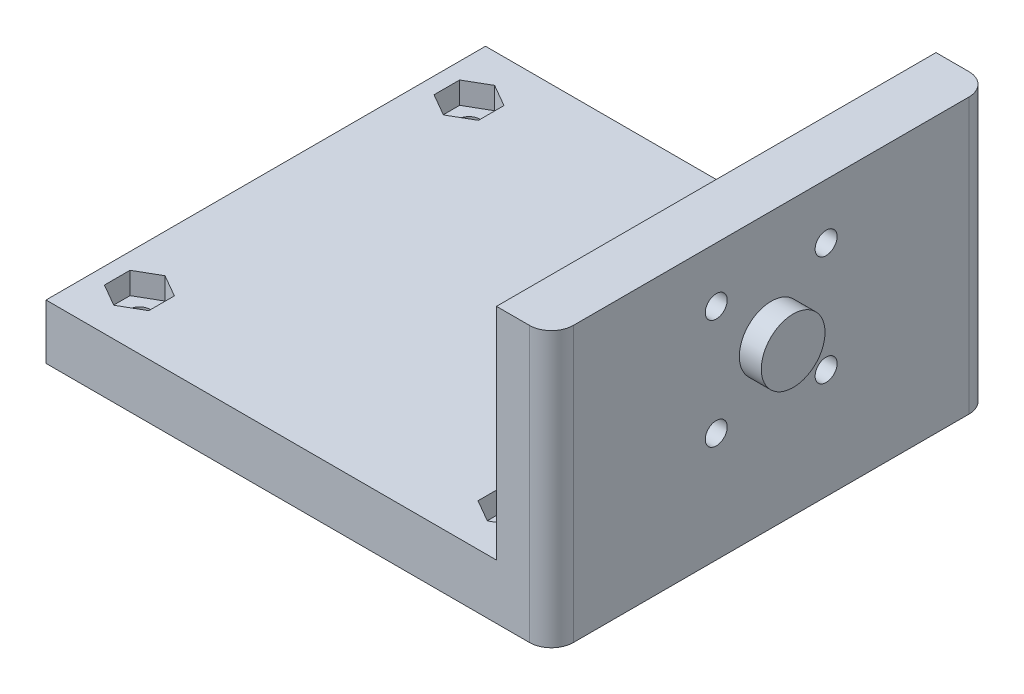
SolidWorks part; units mm, degrees
ref_plane "Plan de face" through (0, 0, 0) normal (0, 0, 1) x (1, 0, 0)
ref_plane "Plan de dessus" through (0, 0, 0) normal (0, 1, 0) x (1, 0, 0)
ref_plane "Plan de droite" through (0, 0, 0) normal (1, 0, 0) x (0, 0, -1)
sketch "Esquisse1" plane through (0, 0, 0) normal (0, 1, 0) x (1, 0, 0)
  line L1 (0, 20) -> (-5, 20)
  line L2 (0, 20) -> (0, -20)
  line L3 (0, -20) -> (-5, -20)
  line L4 (-5, 20) -> (-5, -20)
  dimension "D1" = 5
  dimension "D2" = 40
  dimension "D3" = 20
extrude "Boss.-Extru.1" add sketch "Esquisse1" against normal blind 25
sketch "Esquisse2" plane through (-5, 0, 0) normal (-1, 0, 0) x (0, 0, 1)
  line L0 (-20, -25) -> (-20, 0) construction
  line L1 (20, -25) -> (-20, -25)
  line L2 (20, -25) -> (20, -20)
  line L3 (20, -20) -> (-20, -20)
  line L4 (-20, -25) -> (-20, -20)
  dimension "D1" = 5
extrude "Boss.-Extru.2" add sketch "Esquisse2" along normal blind 41
fillet "Congé1" radius 2 2 edges at (0, -12.5, -20) (0, -12.5, 20)
sketch "Esquisse4" plane through (0, 0, 0) normal (1, 0, 0) x (0, 0, -1)
  circle A0 centre (-5, -5) radius 1
  circle A1 centre (5, -5) radius 1
  circle A2 centre (-5, -15) radius 1
  circle A3 centre (5, -15) radius 1
  dimension "D1" = 10
  dimension "D3" = 2
  dimension "D2" = 10
  dimension "D4" = 5
  dimension "D5" = 5
extrude "Enlèv. mat.-Extru.1" cut sketch "Esquisse4" against normal up to next
sketch "Esquisse5" plane through (0, 0, 0) normal (1, 0, 0) x (0, 0, -1)
  line L1 (-18, 0) -> (18, 0) construction
  line L4 (20, 0) -> (20, -25) construction
  circle A0 centre (0, -10) radius 2.9
  dimension "D1" = 5.8
  dimension "D2" = 10
  dimension "D4" = 20
extrude "Boss.-Extru.3" add sketch "Esquisse5" along normal blind 2
sketch "Esquisse7" plane through (-5, 0, 0) normal (-1, 0, 0) x (0, 0, 1)
  line L1 (-3.835, -7.0178) -> (-2.67, -5)
  line L2 (-2.67, -5) -> (-3.835, -2.9822)
  line L3 (-3.835, -2.9822) -> (-6.165, -2.9822)
  line L4 (-6.165, -2.9822) -> (-7.33, -5)
  line L5 (-7.33, -5) -> (-6.165, -7.0178)
  line L6 (-6.165, -7.0178) -> (-3.835, -7.0178)
  line L7 (3.835, -2.9822) -> (2.67, -5)
  line L8 (2.67, -5) -> (3.835, -7.0178)
  line L9 (3.835, -7.0178) -> (6.165, -7.0178)
  line L10 (6.165, -7.0178) -> (7.33, -5)
  line L11 (7.33, -5) -> (6.165, -2.9822)
  line L12 (6.165, -2.9822) -> (3.835, -2.9822)
  line L13 (-3.835, -17.0178) -> (-2.67, -15)
  line L14 (-2.67, -15) -> (-3.835, -12.9822)
  line L15 (-3.835, -12.9822) -> (-6.165, -12.9822)
  line L16 (-6.165, -12.9822) -> (-7.33, -15)
  line L17 (-7.33, -15) -> (-6.165, -17.0178)
  line L18 (-6.165, -17.0178) -> (-3.835, -17.0178)
  line L19 (7.33, -15) -> (6.165, -12.9822)
  line L20 (6.165, -12.9822) -> (3.835, -12.9822)
  line L21 (3.835, -12.9822) -> (2.67, -15)
  line L22 (2.67, -15) -> (3.835, -17.0178)
  line L23 (3.835, -17.0178) -> (6.165, -17.0178)
  line L24 (6.165, -17.0178) -> (7.33, -15)
  line L25 (18, 0) -> (-18, 0) construction
  line L26 (-20, 0) -> (20, 0) construction
  circle A0 centre (-5, -5) radius 2.0178 construction
  circle A1 centre (5, -5) radius 2.0178 construction
  circle A2 centre (-5, -15) radius 2.0178 construction
  circle A3 centre (5, -15) radius 2.0178 construction
  circle A4 centre (5, -15) radius 1 construction
  dimension "D1" = 2.33
  dimension "D2" = 2.33
  dimension "D3" = 2.33
  dimension "D4" = 2.33
extrude "Enlèv. mat.-Extru.3" cut sketch "Esquisse7" against normal blind 3
sketch "Esquisse9" plane through (0, -20, 0) normal (0, 1, 0) x (1, 0, 0)
  line L0 (-5, -20) -> (-5, 20) construction
  line L1 (-46, -20) -> (-46, 20) construction
  line L4 (-46, -20) -> (-46, 20) construction
  circle A0 centre (-8.5, 15) radius 1
  circle A1 centre (-8.5, -15) radius 1
  circle A2 centre (-42.5, -15) radius 1
  circle A3 centre (-42.5, 15) radius 1
  point P8 (-46, 0)
  dimension "D1" = 2
  dimension "D5" = 15
  dimension "D2" = 3.5
  dimension "D3" = 3.5
  dimension "D4" = 30
extrude "Enlèv. mat.-Extru.5" cut sketch "Esquisse9" against normal through all
sketch "Esquisse8" plane through (0, -20, 0) normal (0, 1, 0) x (1, 0, 0)
  line L0 (-5, -20) -> (-5, 20) construction
  line L1 (-10.5178, 13.835) -> (-8.5, 12.67)
  line L2 (-8.5, 12.67) -> (-6.4822, 13.835)
  line L3 (-6.4822, 13.835) -> (-6.4822, 16.165)
  line L4 (-6.4822, 16.165) -> (-8.5, 17.33)
  line L5 (-8.5, 17.33) -> (-10.5178, 16.165)
  line L6 (-10.5178, 16.165) -> (-10.5178, 13.835)
  line L7 (-10.5178, -16.165) -> (-8.5, -17.33)
  line L8 (-8.5, -17.33) -> (-6.4822, -16.165)
  line L9 (-6.4822, -16.165) -> (-6.4822, -13.835)
  line L10 (-6.4822, -13.835) -> (-8.5, -12.67)
  line L11 (-8.5, -12.67) -> (-10.5178, -13.835)
  line L12 (-10.5178, -13.835) -> (-10.5178, -16.165)
  line L13 (-44.5178, -16.165) -> (-42.5, -17.33)
  line L14 (-42.5, -17.33) -> (-40.4822, -16.165)
  line L15 (-40.4822, -16.165) -> (-40.4822, -13.835)
  line L16 (-40.4822, -13.835) -> (-42.5, -12.67)
  line L17 (-42.5, -12.67) -> (-44.5178, -13.835)
  line L18 (-44.5178, -13.835) -> (-44.5178, -16.165)
  line L19 (-42.5, 12.67) -> (-40.4822, 13.835)
  line L20 (-40.4822, 13.835) -> (-40.4822, 16.165)
  line L21 (-40.4822, 16.165) -> (-42.5, 17.33)
  line L22 (-42.5, 17.33) -> (-44.5178, 16.165)
  line L23 (-44.5178, 16.165) -> (-44.5178, 13.835)
  line L24 (-44.5178, 13.835) -> (-42.5, 12.67)
  circle A0 centre (-8.5, 15) radius 2.0178 construction
  circle A1 centre (-8.5, -15) radius 2.0178 construction
  circle A2 centre (-42.5, -15) radius 2.0178 construction
  circle A3 centre (-42.5, 15) radius 2.0178 construction
  circle A4 centre (-8.5, 15) radius 1 construction
  circle A5 centre (-8.5, -15) radius 1 construction
  circle A7 centre (-42.5, 15) radius 1 construction
  dimension "D1" = 2.33
  dimension "D2" = 2.33
  dimension "D3" = 2.33
  dimension "D4" = 2.33
extrude "Enlèv. mat.-Extru.4" cut sketch "Esquisse8" against normal blind 2
